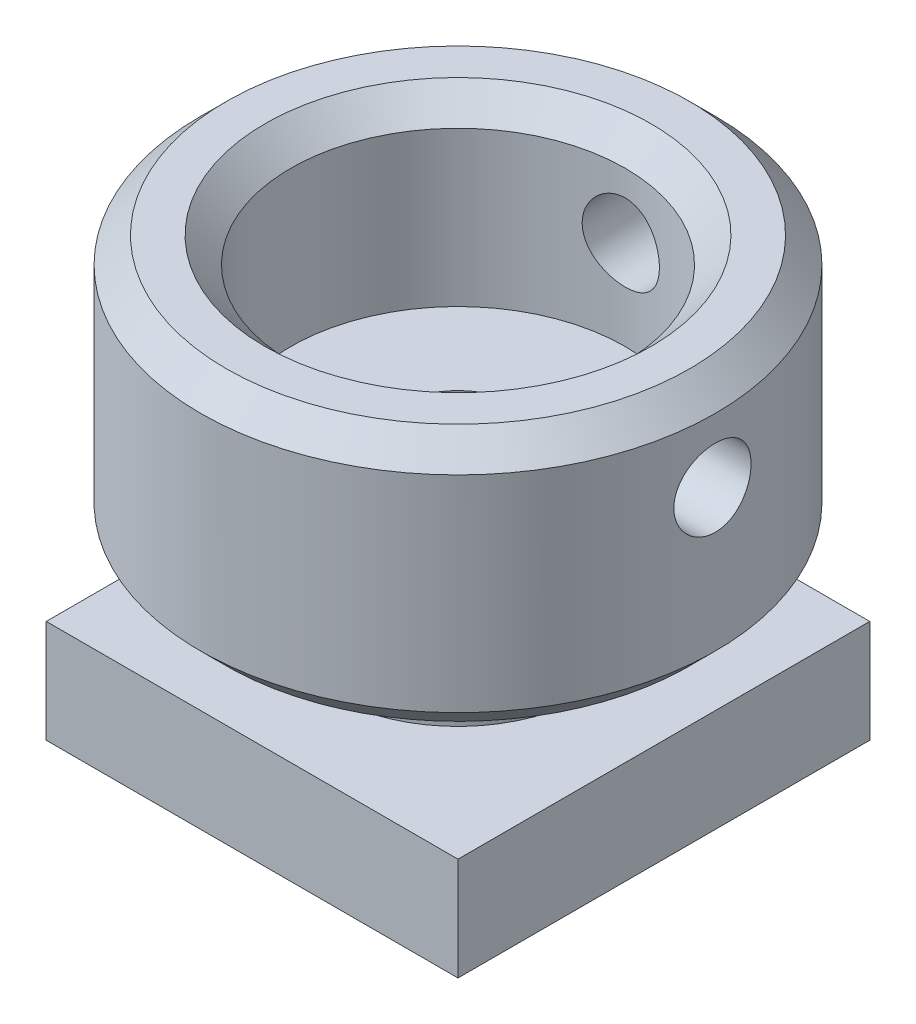
SolidWorks part; units mm, degrees
material "1060 Alloy"
ref_plane "Front Plane" through (0, 0, 0) normal (0, 0, 1) x (1, 0, 0)
ref_plane "Top Plane" through (0, 0, 0) normal (0, 1, 0) x (1, 0, 0)
ref_plane "Right Plane" through (0, 0, 0) normal (1, 0, 0) x (0, 0, -1)
sketch "Sketch1" plane through (0, 0, 0) normal (0, 0, 1) x (1, 0, 0)
  line L0 (0, 0) -> (0, 40.2586) construction
  line L1 (2.5, 0) -> (2.5, 10)
  line L2 (2.5, 10) -> (6.5, 10)
  line L4 (10, 7) -> (5, 7)
  line L5 (5, 7) -> (5, 4)
  line L6 (5, 4) -> (8, 4)
  line L7 (8, 4) -> (8, 0)
  line L8 (8, 0) -> (2.5, 0)
  line L9 (6.5, 10) -> (6.5, 17)
  line L10 (6.5, 17) -> (10, 17)
  line L11 (10, 17) -> (10, 7)
  dimension "D1" = 2.5
  dimension "D2" = 3
  dimension "D3" = 4
  dimension "D4" = 3
  dimension "D5" = 5
  dimension "D6" = 8
  dimension "D7" = 6.5
  dimension "D8" = 10
  dimension "D9" = 7
revolve "Revolve1" add sketch "Sketch1" angle 360 about L0
hole_wizard "Ø3.0 (3) Diameter Hole1" positions "3DSketch1" profile "Sketch3" hole size "Ø3.0" standard "DIN"
sketch3d "3DSketch1"
  line L0 (0, 0, 0) -> (0, 25.9916, 0) construction
  line L2 (0, 13.5, -10) -> (0, 13.5, 0) construction
  line L4 (10, 13.5, 0) -> (0, 13.5, 0) construction
  point P0 (0, 13.5, -10)
  point P2 (10, 13.5, 0)
  dimension "D1" = 3.5
  dimension "D2" = 3.5
sketch "Sketch3" plane through (0, 13.5, -10) normal (1, 0, 0) x (0, 1, 0)
  line L0 (0, 0) -> (0, 12.9013)
  line L1 (0, 12.9013) -> (1.5, 12)
  line L2 (1.5, 12) -> (1.5, 0)
  line L5 (1.5, 0) -> (0, 0)
  line L10 (0, 12.9013) -> (-1.5, 12) construction
  line L11 (0, -6.35) -> (0, 107.95) construction
  dimension "Hole Dia." = 3
  dimension "Hole Depth" = 12
  dimension "Drill Angle" = 118
chamfer "Chamfer1" distance 1 angle 45 2 edges at (0, 7, -10) (0, 17, -10)
chamfer "Chamfer2" distance 1 angle 45 1 edges at (0, 17, -6.5)
sketch "Sketch4" plane through (0, 0, 0) normal (0, -1, 0) x (1, 0, 0)
  line L1 (8, -8) -> (-8, -8)
  line L2 (8, -8) -> (8, 8)
  line L3 (8, 8) -> (-8, 8)
  line L4 (-8, -8) -> (-8, 8)
  circle A0 centre (0, 0) radius 8 construction
  circle A1 centre (0, 0) radius 5.0915
extrude "Extrude1" add sketch "Sketch4" against normal up to surface (4 mm away) up to face at (0, 4, -5)
